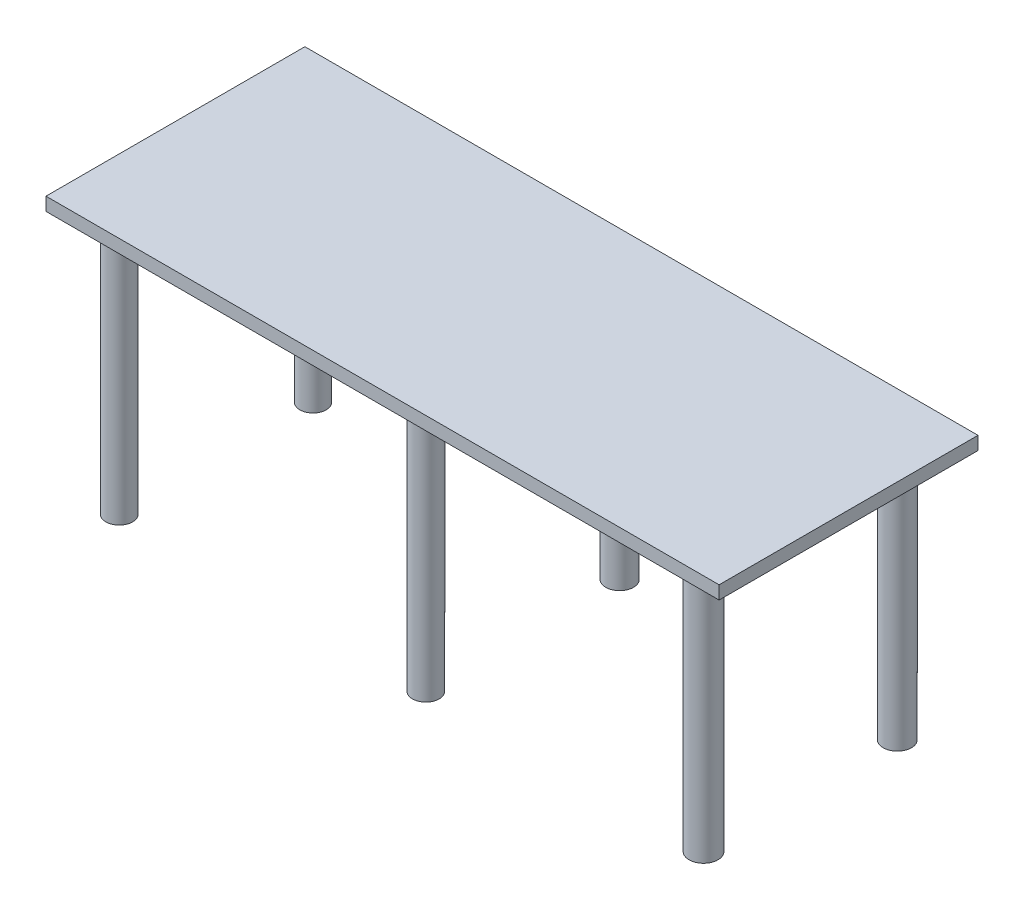
SolidWorks part; units mm, degrees
ref_plane "Alzado" through (0, 0, 0) normal (0, 0, 1) x (1, 0, 0)
ref_plane "Planta" through (0, 0, 0) normal (0, 1, 0) x (1, 0, 0)
ref_plane "Vista lateral" through (0, 0, 0) normal (1, 0, 0) x (0, 0, -1)
sketch "Croquis1" plane through (0, 0, 0) normal (0, 0, 1) x (1, 0, 0)
  line L1 (-683.2006, 149.7321) -> (616.7994, 149.7321)
  line L2 (-683.2006, 149.7321) -> (-683.2006, 124.1964)
  line L3 (-683.2006, 124.1964) -> (616.7994, 124.1964)
  line L4 (616.7994, 149.7321) -> (616.7994, 124.1964)
  dimension "D1" = 1300
extrude "Saliente-Extruir1" add sketch "Croquis1" along normal blind 500
sketch "Croquis2" plane through (0, 124.1964, 0) normal (0, -1, 0) x (1, 0, 0)
  circle A0 centre (-606.0466, 435.691) radius 25.8103
  circle A1 centre (-606.0466, 61.4412) radius 25.3684
  circle A2 centre (-13.8429, 435.691) radius 25.8103
  circle A3 centre (522.4385, 435.691) radius 27.8414
  circle A4 centre (-13.8429, 61.4412) radius 26.7952
  circle A5 centre (522.4385, 61.4412) radius 27.2442
extrude "Saliente-Extruir2" add sketch "Croquis2" along normal blind 500
